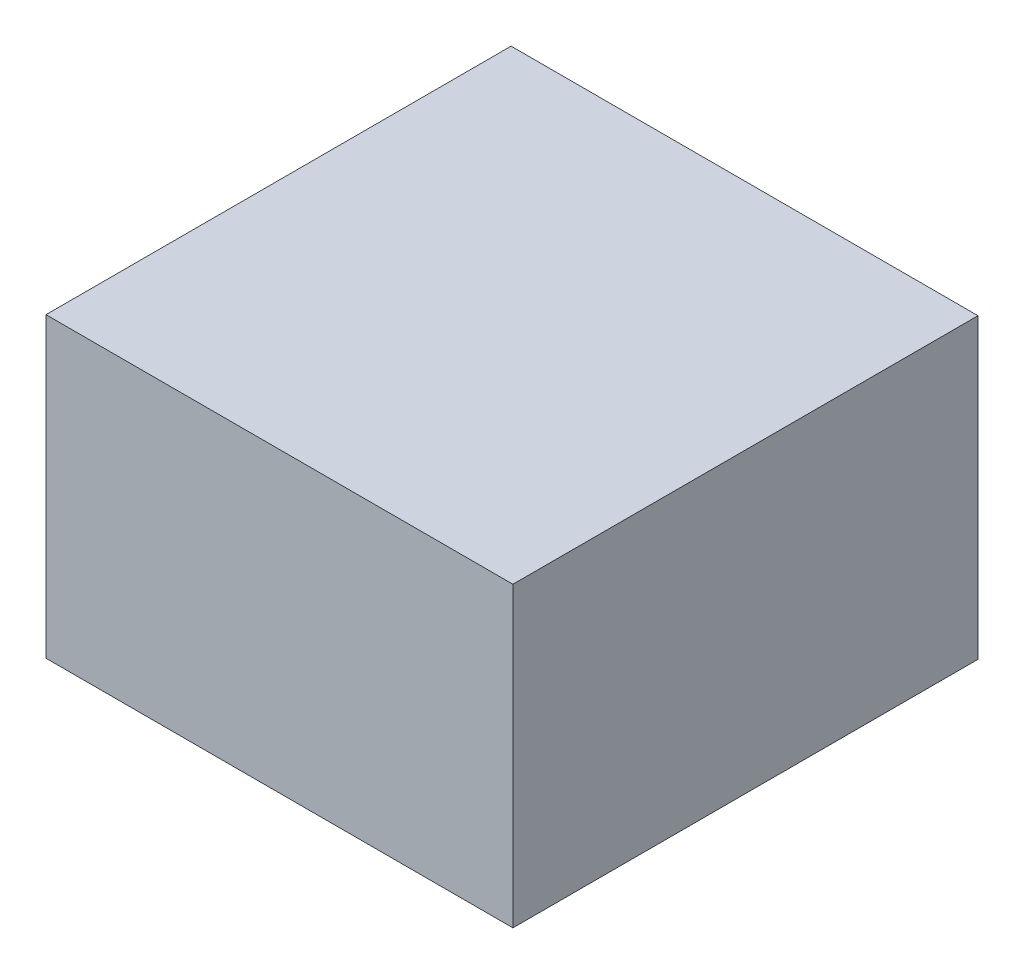
SolidWorks part; units mm, degrees
ref_plane "Front Plane" through (0, 0, 0) normal (0, 0, 1) x (1, 0, 0)
ref_plane "Top Plane" through (0, 0, 0) normal (0, 1, 0) x (1, 0, 0)
ref_plane "Right Plane" through (0, 0, 0) normal (1, 0, 0) x (0, 0, -1)
sketch "Sketch1" plane through (0, 0, 0) normal (0, 1, 0) x (1, 0, 0)
  line L1 (-642.5, 640) -> (642.5, 640)
  line L2 (-642.5, 640) -> (-642.5, -640)
  line L3 (-642.5, -640) -> (642.5, -640)
  line L4 (642.5, 640) -> (642.5, -640)
  line L5 (-642.5, 640) -> (642.5, -640) construction
  line L6 (-642.5, -640) -> (642.5, 640) construction
  point P0 (0, 0)
  point P5 (0, 0)
  dimension "D1" = 1285
  dimension "D2" = 1280
extrude "Boss-Extrude1" add sketch "Sketch1" along normal blind 819
